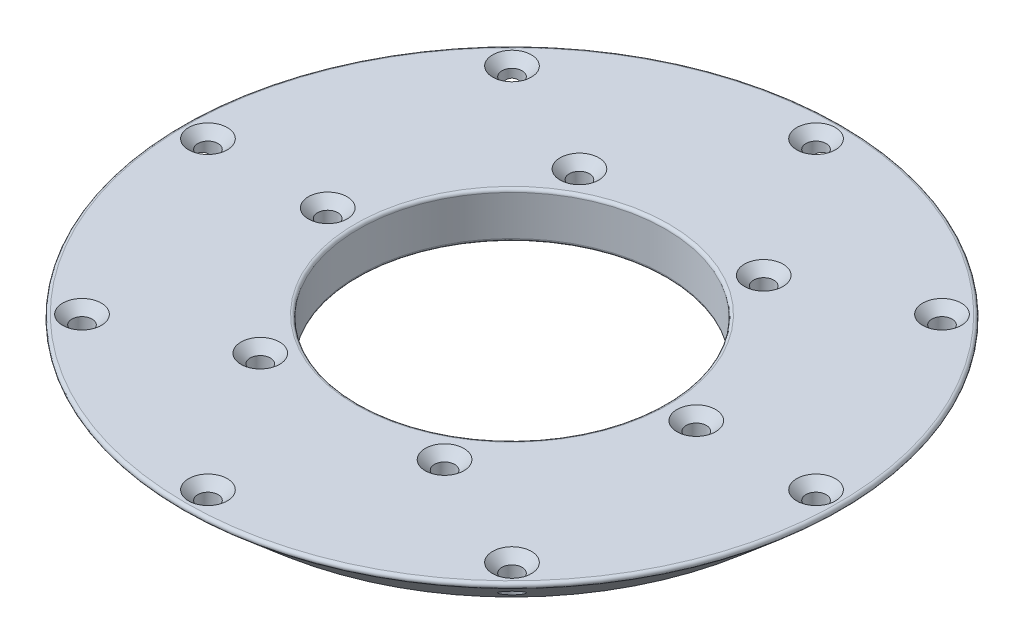
SolidWorks part; units mm, degrees
ref_plane "Front Plane" through (0, 0, 0) normal (0, 0, 1) x (1, 0, 0)
ref_plane "Top Plane" through (0, 0, 0) normal (0, 1, 0) x (1, 0, 0)
ref_plane "Right Plane" through (0, 0, 0) normal (1, 0, 0) x (0, 0, -1)
sketch "Sketch1" plane through (0, 0, 0) normal (0, 0, 1) x (1, 0, 0)
  line L0 (50, 0) -> (91.5822, 0)
  line L1 (106.75, 0) -> (109, 15)
  line L2 (109, 15) -> (50, 15)
  line L3 (0, 0) -> (0, 11.0596) construction
  line L4 (106.75, 0) -> (100, -45) construction
  line L5 (91.5822, 0) -> (109, 15)
  line L6 (50, 15) -> (50, 0)
  line L7 (91.5822, 0) -> (106.4162, -2.2251) construction
  dimension "D1" = 15
  dimension "D2" = 109
  dimension "D3" = 100
  dimension "D4" = 60
  dimension "D5" = 15
  dimension "D6" = 50
revolve "Revolve1" add sketch "Sketch1" angle 360 about L3
hole_wizard "CSK for M6 Flat Head Machine Screw1" positions "Sketch3" profile "Sketch2" countersink size "M6" standard "Ansi Metric" end condition up to next
sketch "Sketch3" plane through (0, 15, 0) normal (0, 1, 0) x (-1, 0, 0)
  point P0 (-99, 0)
  dimension "D1" = 99
sketch "Sketch2" plane through (99, 15, 0) normal (1, 0, 0) x (0, 0, 1)
  line L0 (0, 0) -> (0, 15.001)
  line L1 (0, 15.001) -> (3.3, 15.001)
  line L2 (3.3, 15.001) -> (3.3, 3)
  line L3 (3.3, 3) -> (6.3, 0)
  line L5 (6.3, 0) -> (0, 0)
  line L6 (-3.3, 3) -> (-6.3, 0) construction
  line L11 (0, -6.35) -> (0, 107.95) construction
  dimension "Thru Hole Dia." = 6.6
  dimension "Thru Hole Depth" = 15.001
  dimension "Near C'Sink Dia." = 12.6
  dimension "Near C'Sink Angle" = 90
hole_wizard "CSK for M6 Flat Head Machine Screw2" positions "3DSketch1" profile "Sketch4" countersink size "M6" standard "Ansi Metric" end condition through all
sketch3d "3DSketch1"
  line L4 (0, 15, 0) -> (60, 15, 0) construction
  line L5 (0, 15, 0) -> (0, 0, 0) construction
  point P2 (60, 15, 0)
  dimension "D1" = 60
sketch "Sketch4" plane through (60, 15, 0) normal (1, 0, 0) x (0, 0, 1)
  line L0 (0, 0) -> (0, 15)
  line L1 (0, 15) -> (3.3, 15)
  line L2 (3.3, 15) -> (3.3, 3)
  line L3 (3.3, 3) -> (6.3, 0)
  line L5 (6.3, 0) -> (0, 0)
  line L6 (-3.3, 3) -> (-6.3, 0) construction
  line L11 (0, -6.35) -> (0, 107.95) construction
  dimension "Thru Hole Dia." = 6.6
  dimension "Thru Hole Depth" = 15
  dimension "Near C'Sink Dia." = 12.6
  dimension "Near C'Sink Angle" = 90
pattern_circular "CirPattern1" count 8 over 360 about axis through (0, 0, 0) along (0, 1, 0) of "CSK for M6 Flat Head Machine Screw1"
pattern_circular "CirPattern2" count 6 over 360 about axis through (0, 0, 0) along (0, 1, 0) of "CSK for M6 Flat Head Machine Screw2"
fillet "Finishing Fillet" radius 1 3 edges at (0, 15, -50) (0, 0, -50) (0, 15, -109)
